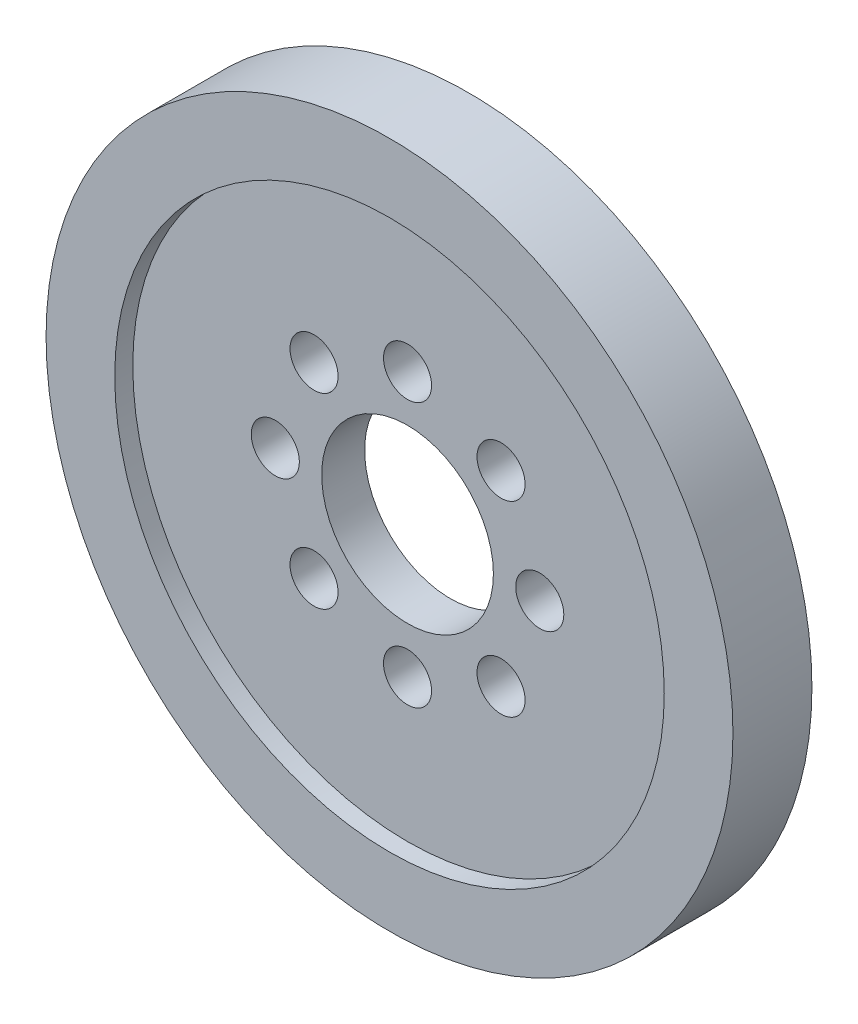
SolidWorks part; units mm, degrees
ref_plane "Front Plane" through (0, 0, 0) normal (0, 0, 1) x (1, 0, 0)
ref_plane "Top Plane" through (0, 0, 0) normal (0, 1, 0) x (1, 0, 0)
ref_plane "Right Plane" through (0, 0, 0) normal (1, 0, 0) x (0, 0, -1)
sketch "Sketch1" plane through (0, 0, 0) normal (0, 0, 1) x (1, 0, 0)
  circle A0 centre (0, 0) radius 25.4
  circle A1 centre (0, 0) radius 20.32
  dimension "D1" = 50.8
  dimension "D2" = 40.64
extrude "Boss-Extrude1" add sketch "Sketch1" along normal mid plane 5.842
sketch "Sketch3" plane through (0, 0, 0) normal (0, 0, 1) x (1, 0, 0)
  circle A0 centre (0, 0) radius 20.32
  circle A1 centre (0, 0) radius 6.35
  circle A2 centre (0, 9.779) radius 1.778
  circle A3 centre (6.9148, 6.9148) radius 1.778
  circle A4 centre (9.779, 0) radius 1.778
  circle A5 centre (6.9148, -6.9148) radius 1.778
  circle A6 centre (0, -9.779) radius 1.778
  circle A7 centre (-6.9148, -6.9148) radius 1.778
  circle A8 centre (-9.779, 0) radius 1.778
  circle A9 centre (-6.9148, 6.9148) radius 1.778
  dimension "D1" = 12.7
  dimension "D2" = 3.556
  dimension "D3" = 9.779
  dimension "D4" = 8
extrude "Boss-Extrude2" add sketch "Sketch3" along normal mid plane 3.175
